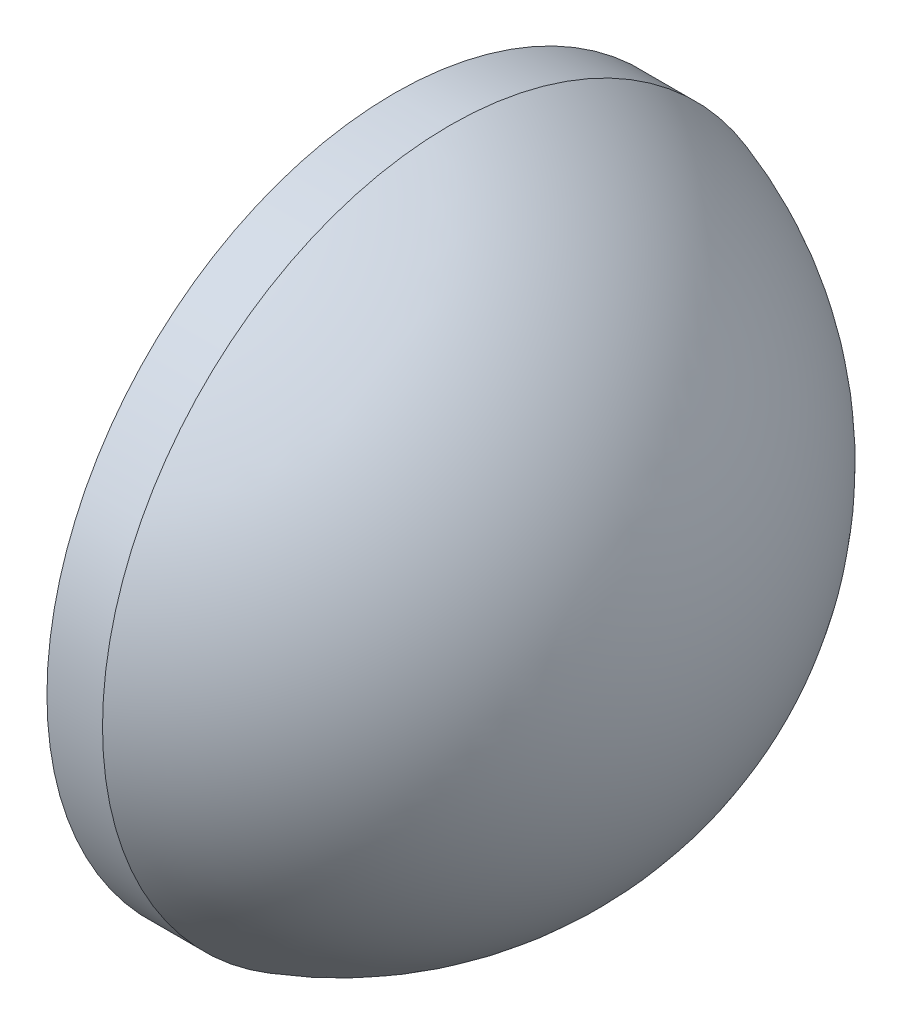
SolidWorks part; units mm, degrees
ref_plane "前视基准面" through (0, 0, 0) normal (0, 0, 1) x (1, 0, 0)
ref_plane "上视基准面" through (0, 0, 0) normal (0, 1, 0) x (1, 0, 0)
ref_plane "右视基准面" through (0, 0, 0) normal (1, 0, 0) x (0, 0, -1)
sketch "草图1" plane through (0, 0, 0) normal (0, 0, 1) x (1, 0, 0)
  line L0 (203.7724, -102.6914) -> (217.2181, -102.6914) construction
  line L1 (205.2844, -102.6914) -> (205.2844, -90.1914)
  line L2 (216.4444, -102.6914) -> (205.2844, -102.6914)
  line L5 (205.2844, -90.1914) -> (207.2844, -90.1914)
  arc A0 (216.4444, -102.6914) -> (207.2844, -90.1914) centre (203.3355, -102.6914) ccw
revolve "旋转1" add sketch "草图1" angle 360 about L0
